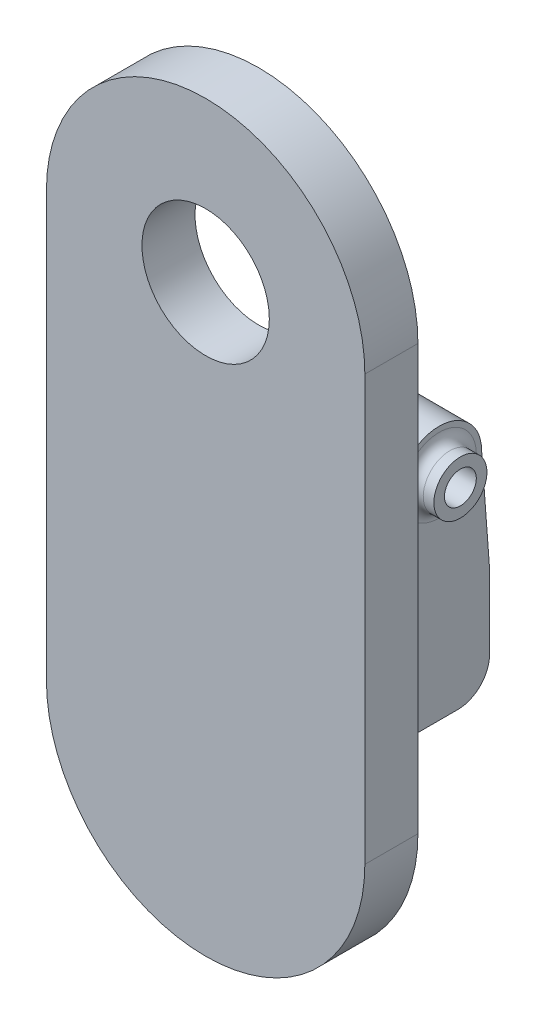
SolidWorks part; units mm, degrees
ref_plane "Front Plane" through (0, 0, 0) normal (0, 0, 1) x (1, 0, 0)
ref_plane "Top Plane" through (0, 0, 0) normal (0, 1, 0) x (1, 0, 0)
ref_plane "Right Plane" through (0, 0, 0) normal (1, 0, 0) x (0, 0, -1)
sketch "Sketch1" plane through (0, 0, 0) normal (0, 0, 1) x (1, 0, 0)
  line L0 (0, 40.5052) -> (0, -50.331) construction
  line L1 (-54.7196, 0) -> (37.5722, 0) construction
  line L2 (15, 0) -> (15, -40)
  line L3 (15, -40) -> (-15, -40) construction
  line L4 (-15, -40) -> (-15, 0)
  circle A0 centre (0, 0) radius 6
  arc A1 (15, 0) -> (-15, 0) centre (0, 0) ccw
  arc A2 (-15, -40) -> (15, -40) centre (0, -40) ccw
  dimension "D1" = 12
  dimension "D2" = 15
  dimension "D3" = 40
extrude "Boss-Extrude1" add sketch "Sketch1" along normal blind 5
sketch "Sketch2" plane through (0, 0, 0) normal (0, 0, -1) x (-1, 0, 0)
  line L0 (0, 50.6594) -> (0, -68.3456) construction
  line L1 (30.9949, -42) -> (-29.8469, -42) construction
  line L2 (43.7499, 0) -> (-41.9642, 0) construction
  line L3 (3.25, -40) -> (3.25, -50)
  line L4 (3.25, -50) -> (8.25, -50)
  line L5 (8.25, -50) -> (8.25, -40)
  line L6 (8.25, -40) -> (3.25, -40)
  line L7 (1.25, -45.1838) -> (1.25, -44.9891) construction
  dimension "D1" = 42
  dimension "D2" = 40
  dimension "D3" = 10
  dimension "D4" = 5
  dimension "D5" = 2
extrude "Boss-Extrude2" add sketch "Sketch2" along normal blind 25
sketch "Sketch3" plane through (-3.25, 0, 0) normal (1, 0, 0) x (0, 0, -1)
  line L0 (20.25, -30) -> (20.25, -53.3219) construction
  line L1 (39.4011, -30) -> (13.3774, -30) construction
  line L2 (24.25, -30) -> (25, -40)
  line L3 (16.25, -30) -> (15.5, -40)
  line L6 (15.5, -40) -> (25, -40)
  arc A0 (24.25, -30) -> (16.25, -30) centre (20.25, -30) ccw
  circle A1 centre (20.25, -30) radius 1.5
  dimension "D1" = 4
  dimension "D2" = 3
extrude "Boss-Extrude3" add sketch "Sketch3" against normal blind 5
sketch "Sketch4" plane through (0, -50, 0) normal (0, -1, 0) x (1, 0, 0)
  line L0 (-8.25, -25) -> (-8.25, 0)
  line L1 (-8.25, -25) -> (-8.25, 0) construction
  line L2 (-15, 0) -> (15, 0) construction
  line L3 (-8.25, 0) -> (-10.25, 0)
  line L4 (-10.25, 0) -> (-8.25, -25)
  dimension "D1" = 2
extrude "Boss-Extrude4" add sketch "Sketch4" against normal blind 8
sketch "Sketch5" plane through (-8.25, 0, 0) normal (-1, 0, 0) x (0, 0, 1)
  line L3 (-24.25, -30) -> (-25, -40)
  line L4 (0, -40) -> (-15.5, -40)
  line L5 (-15.5, -40) -> (-16.25, -30)
  line L6 (-24.25, -30) -> (-25, -40)
  line L7 (0, -40) -> (-15.5, -40)
  line L8 (-15.5, -40) -> (-16.25, -30)
  line L12 (-25, -40) -> (-25, -42)
  line L13 (-25, -40) -> (-25, -42)
  line L14 (-25, -42) -> (0, -42)
  line L15 (-25, -42) -> (0, -42)
  line L16 (0, -42) -> (0, -40)
  line L17 (0, -42) -> (0, -40)
  circle A0 centre (-20.25, -30) radius 1.5 construction
  arc A1 (-16.25, -30) -> (-24.25, -30) centre (-20.25, -30) ccw
  arc A2 (-16.25, -30) -> (-24.25, -30) centre (-20.25, -30) ccw
  circle A3 centre (-20.25, -30) radius 1.5
  dimension "D1" = 0
extrude "Boss-Extrude5" add sketch "Sketch5" along normal up to surface (0.76 mm away)
sketch "Sketch6" plane through (-3.25, 0, 0) normal (1, 0, 0) x (0, 0, -1)
  circle A0 centre (20.25, -30) radius 1.5
  circle A1 centre (20.25, -30) radius 2.5
  dimension "D1" = 3
  dimension "D2" = 5
extrude "Boss-Extrude6" add sketch "Sketch6" along normal blind 2
fillet "Fillet1" radius 1 1 edges at (-3.25, -32.5, -20.25)
fillet "Fillet2" radius 3 2 edges at (-6.13, -40, -15.5) (-5.75, -50, -25)
